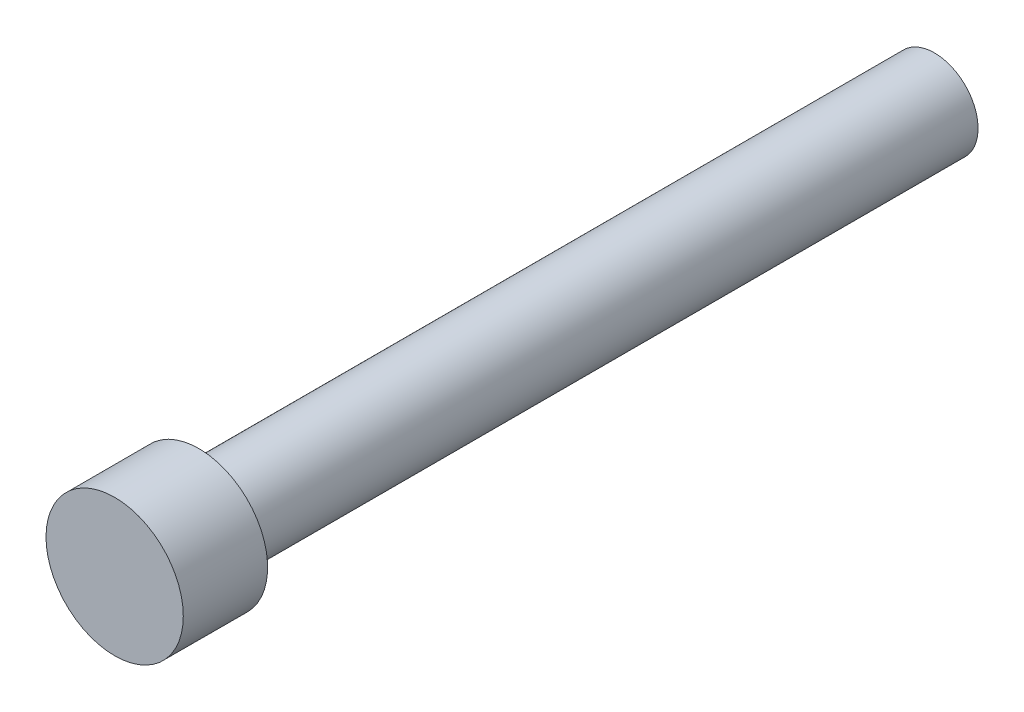
SolidWorks part; units mm, degrees
ref_plane "Front Plane" through (0, 0, 0) normal (0, 0, 1) x (1, 0, 0)
ref_plane "Top Plane" through (0, 0, 0) normal (0, 1, 0) x (1, 0, 0)
ref_plane "Right Plane" through (0, 0, 0) normal (1, 0, 0) x (0, 0, -1)
sketch "Sketch1" plane through (0, 0, 0) normal (0, 0, 1) x (1, 0, 0)
  circle A0 centre (0, 0) radius 1.778
extrude "Extrude1" add sketch "Sketch1" along normal blind 21.2344
sketch "Sketch3" plane through (0, 0, 0) normal (0, 0, -1) x (-1, 0, 0)
  circle A0 centre (0, 0) radius 1.1303
extrude "Extrude2" cut sketch "Sketch3" against normal blind 19.05 flip side to cut
